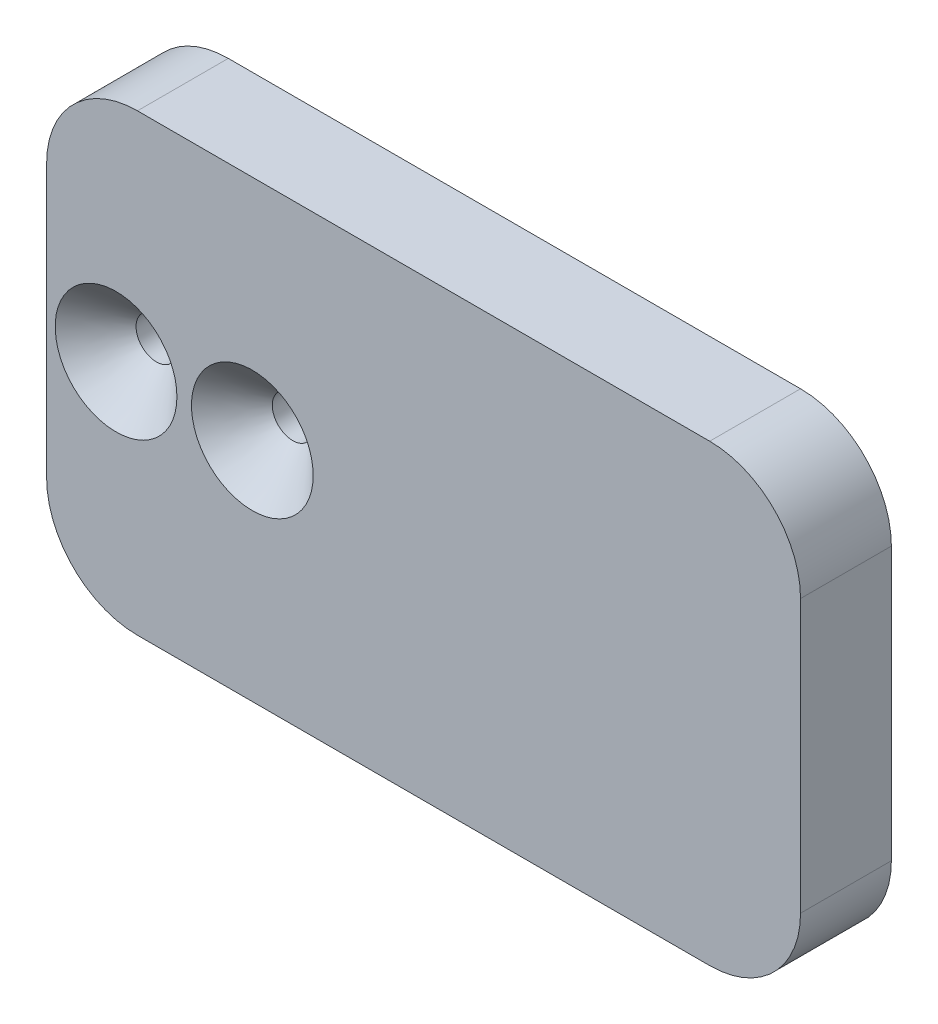
SolidWorks part; units mm, degrees
ref_plane "Front Plane" through (0, 0, 0) normal (0, 0, 1) x (1, 0, 0)
ref_plane "Top Plane" through (0, 0, 0) normal (0, 1, 0) x (1, 0, 0)
ref_plane "Right Plane" through (0, 0, 0) normal (1, 0, 0) x (0, 0, -1)
ref_plane "Reference Plane" through (0, 0, 0) normal (0, 0, 1) x (1, 0, 0)
ref_plane "Platform Height" through (0, 0, 25) normal (0, 0, 1) x (1, 0, 0)
ref_plane "Base extension" through (39.6398, 0, 0) normal (1, 0, 0) x (0, 0, -1)
sketch "Sketch2" plane through (0, 0, 0) normal (0, 0, 1) x (1, 0, 0)
  line L1 (-43.3602, 16.5187) -> (-13.3602, 16.5187)
  line L2 (-43.3602, 16.5187) -> (-43.3602, -3.4813)
  line L3 (-43.3602, -3.4813) -> (-13.3602, -3.4813)
  line L4 (-13.3602, 16.5187) -> (-13.3602, -3.4813)
  line L5 (-60.4147, 6.5187) -> (63.1287, 6.5187) construction
  line L6 (-40.3602, 12.8187) -> (-40.3602, 0.2187) construction
  line L7 (-28.3602, 23.0385) -> (-28.3602, -14.6964) construction
  point P7 (-40.3602, 6.5187)
  point P8 (-43.3602, 6.5187)
  dimension "D1" = 30
  dimension "D2" = 20
  dimension "D3" = 15
  dimension "D4" = 3
extrude "Boss-Extrude1" add sketch "Sketch2" along normal up to surface (25 mm away) up to plane "Platform Height"
sketch "Sketch3" plane through (0, 0, 25) normal (0, 0, 1) x (1, 0, 0)
  line L0 (-66.2092, 6.5187) -> (80.0477, 6.5187) construction
  line L1 (39.6398, -29.8911) -> (39.6398, 29.8911) construction
  line L3 (39.6398, -18.4813) -> (-43.3602, -18.4813)
  line L6 (39.6398, -18.4813) -> (39.6398, 31.5187)
  line L7 (39.6398, 31.5187) -> (-43.3602, 31.5187)
  line L8 (-43.3602, -18.4813) -> (-43.3602, 31.5187)
  line L9 (39.6398, -18.4813) -> (-43.3602, 31.5187) construction
  line L10 (39.6398, 31.5187) -> (-43.3602, -18.4813) construction
  line L11 (-43.3602, 16.5187) -> (-43.3602, -3.4813) construction
  line L12 (-13.3602, -3.4813) -> (-13.3602, 16.5187) construction
  point P2 (-1.8602, 6.5187)
  point P12 (-13.3602, 6.5187)
  dimension "D1" = 50
extrude "Boss-Extrude2" add sketch "Sketch3" against normal blind 10
sketch "Sketch6" plane through (0, 0, 25) normal (0, 0, 1) x (1, 0, 0)
  line L0 (-35.7149, 6.4219) -> (-20.7149, 6.4219) construction
  circle A0 centre (-35.7149, 6.4219) radius 2.4218 construction
  circle A1 centre (-20.7149, 6.4219) radius 2.2246 construction
  arc A2 (-38.2749, 6.4199) -> (-38.2749, 6.4237) centre (-35.7149, 6.4219) ccw construction
  arc A3 (-22.8319, 6.4202) -> (-22.8319, 6.4233) centre (-20.7149, 6.4219) ccw construction
sketch "Sketch9" plane through (0, 0, 25) normal (0, 0, 1) x (1, 0, 0)
  point P0 (-35.7149, 6.4219)
  point P3 (-20.7149, 6.4219)
hole_wizard "CSK for M4 Flat Head Machine Screw1" positions "Sketch9" profile "Sketch8" countersink size "M4" standard "ANSI Metric" end condition through all
sketch "Sketch8" plane through (-35.7149, 6.4219, 25) normal (1, 0, 0) x (0, -1, 0)
  line L0 (0, 0) -> (0, 25)
  line L1 (0, 25) -> (2.25, 25)
  line L2 (2.25, 25) -> (2.25, 4.45)
  line L3 (2.25, 4.45) -> (6.7, 0)
  line L5 (6.7, 0) -> (0, 0)
  line L6 (-2.25, 4.45) -> (-6.7, 0) construction
  line L11 (0, -6.35) -> (0, 107.95) construction
  dimension "Thru Hole Dia." = 4.5
  dimension "Thru Hole Depth" = 25
  dimension "Near C'Sink Dia." = 13.4
  dimension "Near C'Sink Angle" = 90
fillet "Fillet1" radius 10 4 edges at (39.6398, 31.5187, 20) (39.6398, -18.4813, 20) (-43.3602, -18.4813, 20) (-43.3602, 31.5187, 20)
fillet "Fillet2" radius 10 3 edges at (-28.3602, -3.4813, 15) (-13.3602, 6.5187, 15) (-28.3602, 16.5187, 15)
fillet "Fillet3" radius 3 4 edges at (-13.3602, 6.5187, 0) (-28.3602, -3.4813, 0) (-28.3602, 16.5187, 0) (-43.3602, 6.5187, 0)
